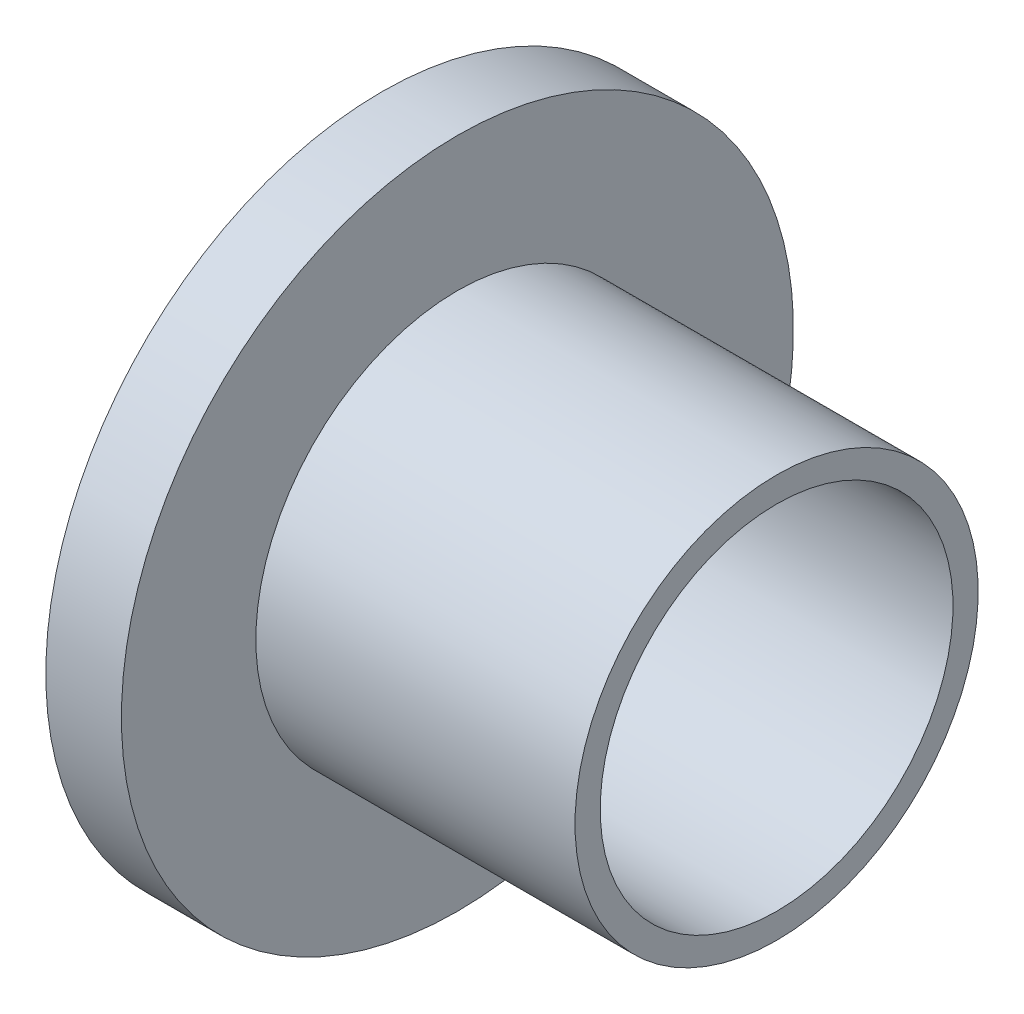
SolidWorks part; units mm, degrees
ref_plane "Front Plane" through (0, 0, 0) normal (0, 0, 1) x (1, 0, 0)
ref_plane "Top Plane" through (0, 0, 0) normal (0, 1, 0) x (1, 0, 0)
ref_plane "Right Plane" through (0, 0, 0) normal (1, 0, 0) x (0, 0, -1)
sketch "Sketch1" plane through (0, 0, 0) normal (0, 0, 1) x (1, 0, 0)
  line L0 (104.4593, 320.507) -> (289.7927, 320.507) construction
sketch "Sketch2" plane through (0, 0, 0) normal (0, 0, 1) x (1, 0, 0)
  line L0 (177.8333, 227) -> (889.1667, 227) construction
  line L1 (33.5, 227) -> (167.5, 227) construction
  line L2 (33.5, 227) -> (167.5, 227) construction
  line L10 (0, 90.0846) -> (6.001, 90.0846)
  line L11 (0, 53.0847) -> (46.998, 53.0847) construction
  line L12 (0, 93.0846) -> (9.001, 93.0846)
  line L14 (6.001, 90.0846) -> (6.001, 74.0831)
  line L15 (9.001, 93.0846) -> (9.001, 77.0831)
  line L16 (9.001, 77.0831) -> (46.998, 77.0831)
  line L17 (6.001, 74.0831) -> (46.998, 74.0831)
  line L18 (0, 93.0846) -> (0, 90.0846)
  line L19 (46.998, 77.0831) -> (46.998, 74.0831)
revolve "Revolve1" add sketch "Sketch2" angle 360 about L11
